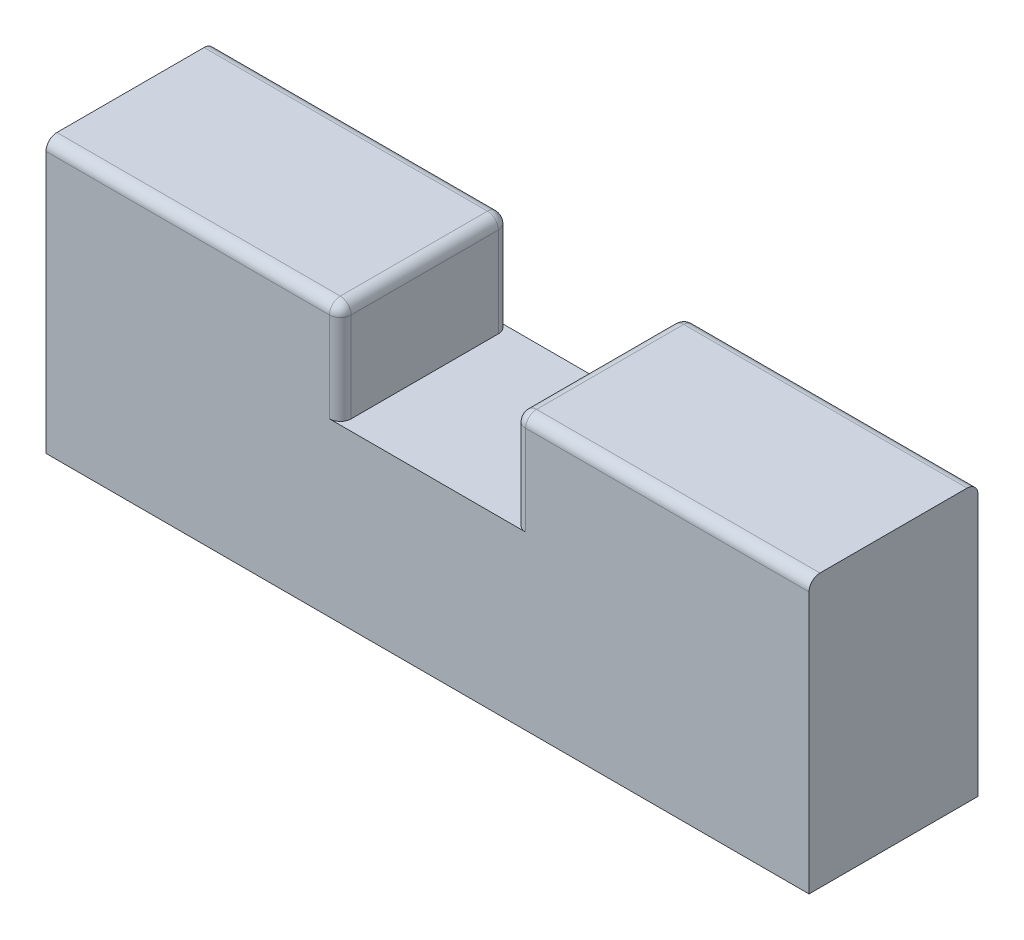
SolidWorks part; units mm, degrees
material "Cedar"
ref_plane "Front Plane" through (0, 0, 0) normal (0, 0, 1) x (1, 0, 0)
ref_plane "Top Plane" through (0, 0, 0) normal (0, 1, 0) x (1, 0, 0)
ref_plane "Right Plane" through (0, 0, 0) normal (1, 0, 0) x (0, 0, -1)
sketch "Sketch1" plane through (0, 0, 0) normal (1, 0, 0) x (0, 0, -1)
  line L1 (-7.75, -12.5) -> (7.75, -12.5)
  line L2 (-7.75, -12.5) -> (-7.75, 12.5)
  line L3 (-7.75, 12.5) -> (7.75, 12.5)
  line L4 (7.75, -12.5) -> (7.75, 12.5)
  line L5 (-7.75, -12.5) -> (7.75, 12.5) construction
  line L6 (-7.75, 12.5) -> (7.75, -12.5) construction
  point P0 (0, 0)
  dimension "D1" = 15.5
  dimension "D2" = 25
extrude "Boss-Extrude1" add sketch "Sketch1" along normal mid plane 70
sketch "Sketch2" plane through (0, 0, 7.75) normal (0, 0, 1) x (1, 0, 0)
  line L0 (35, 12.5) -> (-35, 12.5) construction
  line L1 (-8, 21.75) -> (8, 21.75)
  line L2 (-8, 21.75) -> (-8, 3.25)
  line L3 (-8, 3.25) -> (8, 3.25)
  line L4 (8, 21.75) -> (8, 3.25)
  line L5 (-8, 21.75) -> (8, 3.25) construction
  line L6 (-8, 3.25) -> (8, 21.75) construction
  point P0 (0, 12.5)
  dimension "D1" = 18.5
  dimension "D2" = 16
extrude "Cut-Extrude1" cut sketch "Sketch2" against normal through all
fillet "Fillet1" radius 1 2 edges at (8, 12.5, 0) (-8, 12.5, 0)
fillet "Fillet2" radius 1 12 edges at (8, 7.375, 7.75) (8.2929, 12.2071, 7.75) (8, 7.375, -7.75) (8.2929, 12.2071, -7.75) (-8, 7.375, -7.75) (-8.2929, 12.2071, -7.75) (-8, 7.375, 7.75) (-8.2929, 12.2071, 7.75) (22, 12.5, 7.75) (22, 12.5, -7.75) (-22, 12.5, -7.75) (-22, 12.5, 7.75)
